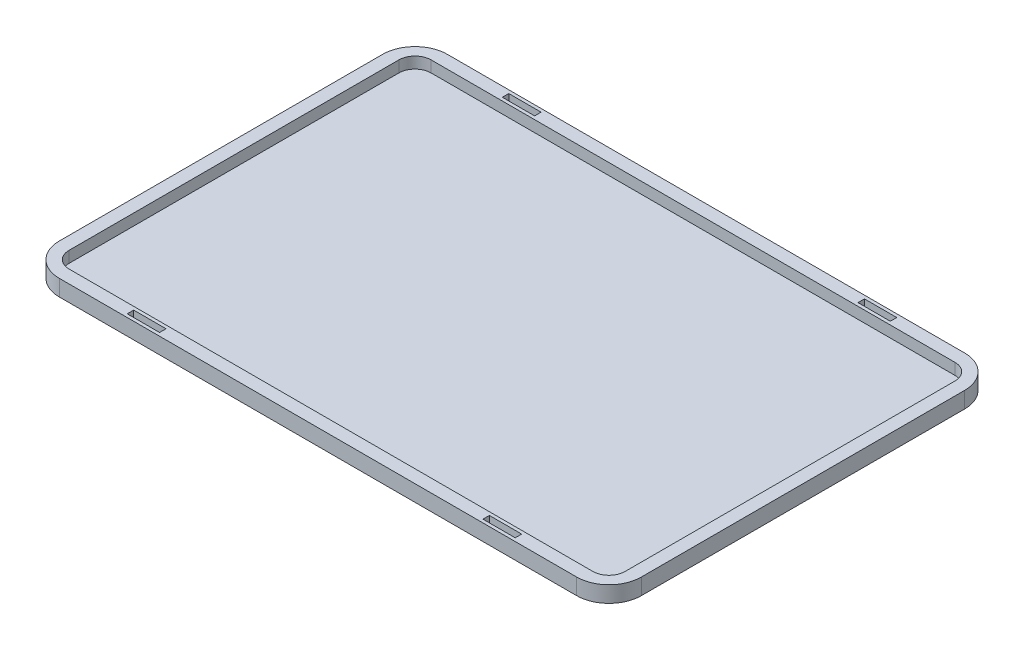
SolidWorks part; units mm, degrees
ref_plane "Front Plane" through (0, 0, 0) normal (0, 0, 1) x (1, 0, 0)
ref_plane "Top Plane" through (0, 0, 0) normal (0, 1, 0) x (1, 0, 0)
ref_plane "Right Plane" through (0, 0, 0) normal (1, 0, 0) x (0, 0, -1)
sketch "Sketch1" plane through (0, 0, 0) normal (0, 1, 0) x (1, 0, 0)
  line L1 (-90, -60) -> (90, -60)
  line L2 (-90, -60) -> (-90, 60)
  line L3 (-90, 60) -> (90, 60)
  line L4 (90, -60) -> (90, 60)
  line L5 (-90, -60) -> (90, 60) construction
  line L6 (-90, 60) -> (90, -60) construction
  point P0 (0, 0)
extrude "Boss-Extrude1" add sketch "Sketch1" along normal blind 5
fillet "Fillet1" radius 10 1 edges at (-90, 2.5, 60)
fillet "Fillet2" radius 10 1 edges at (90, 2.5, 60)
fillet "Fillet3" radius 10 1 edges at (90, 2.5, -60)
fillet "Fillet4" radius 10 1 edges at (-90, 2.5, -60)
shell "Shell1" thickness 4
ref_plane "Plane1" through (0, 10, 0) normal (0, 1, 0) x (1, 0, 0)
sketch "Sketch6" plane through (0, 10, 0) normal (0, 1, 0) x (1, 0, 0)
  line L0 (80, 56) -> (-80, 56) construction
  line L1 (-86, -56) -> (86, -56)
  line L2 (-86, -56) -> (-86, 56)
  line L3 (-86, 56) -> (86, 56)
  line L4 (86, -56) -> (86, 56)
  line L5 (-86, -56) -> (86, 56) construction
  line L6 (-86, 56) -> (86, -56) construction
  line L7 (-86, 50) -> (-86, -50) construction
  line L8 (-80, -56) -> (80, -56) construction
  line L9 (86, -50) -> (86, 50) construction
  point P0 (0.9901, -0.6447)
extrude "Cut-Extrude1" cut sketch "Sketch6" against normal blind 8.5
fillet "Fillet5" radius 5 1 edges at (-86, 3.25, -56)
fillet "Fillet6" radius 5 1 edges at (86, 3.25, -56)
fillet "Fillet7" radius 5 1 edges at (-86, 3.25, 56)
fillet "Fillet8" radius 5 1 edges at (86, 3.25, 56)
sketch "Sketch8" plane through (0, 0, 0) normal (0, 1, 0) x (1, 0, 0)
  line L0 (-60, 94.0427) -> (-60, -89.9713) construction
  line L1 (-50, 94.0427) -> (-50, -89.9713) construction
  line L2 (50, 96.8451) -> (50, -95.1063) construction
  line L3 (60, 96.8451) -> (60, -95.1063) construction
  line L4 (-90, 50) -> (-90, -50) construction
  line L5 (90, -50) -> (90, 50) construction
  line L6 (80, 60) -> (-80, 60) construction
  line L7 (-60, 59) -> (-50, 59)
  line L8 (-60, 59) -> (-60, 57)
  line L9 (-60, 57) -> (-50, 57)
  line L10 (-50, 59) -> (-50, 57)
  line L11 (81, 56) -> (-81, 56) construction
  line L12 (-81, -56) -> (81, -56) construction
  line L13 (50, 59) -> (60, 59)
  line L14 (50, 59) -> (50, 57)
  line L15 (50, 57) -> (60, 57)
  line L16 (60, 59) -> (60, 57)
  line L17 (50, -57) -> (60, -57)
  line L18 (50, -57) -> (50, -59)
  line L19 (50, -59) -> (60, -59)
  line L20 (60, -57) -> (60, -59)
  line L21 (-80, -60) -> (80, -60) construction
  line L23 (-60, -57) -> (-50, -57)
  line L24 (-60, -57) -> (-60, -59)
  line L25 (-60, -59) -> (-50, -59)
  line L26 (-50, -57) -> (-50, -59)
  dimension "D1" = 30
  dimension "D2" = 40
  dimension "D3" = 30
  dimension "D4" = 40
  dimension "D5" = 1
  dimension "D6" = 1
  dimension "D7" = 1
  dimension "D8" = 1
extrude "Cut-Extrude2" cut sketch "Sketch8" along normal blind 8
